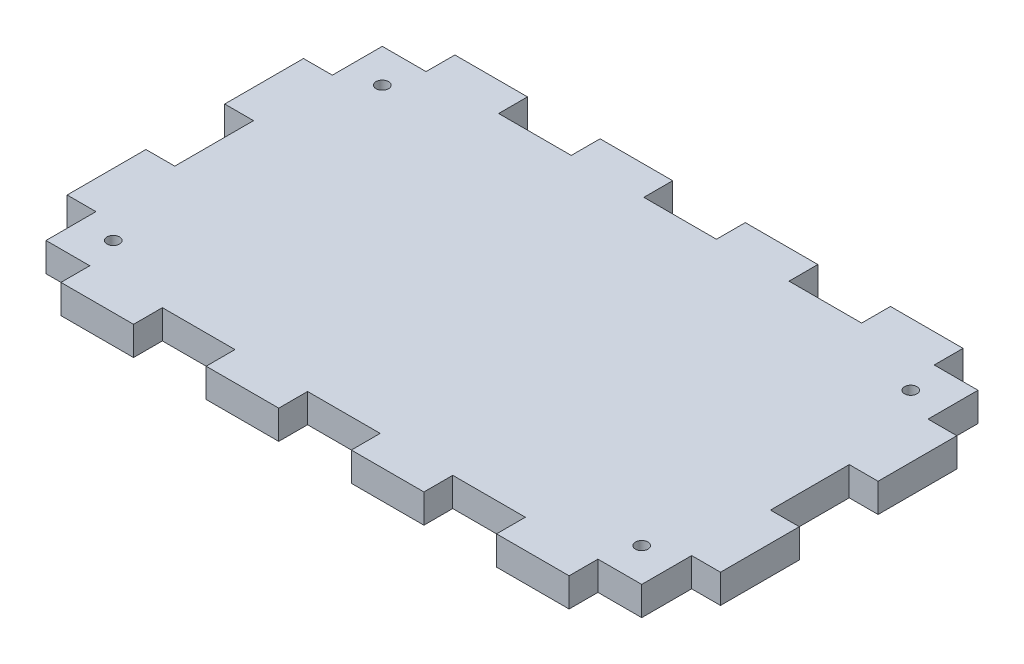
SolidWorks part; units mm, degrees
ref_plane "Front" through (0, 0, 0) normal (0, 0, 1) x (1, 0, 0)
ref_plane "Top" through (0, 0, 0) normal (0, 1, 0) x (1, 0, 0)
ref_plane "Right" through (0, 0, 0) normal (1, 0, 0) x (0, 0, -1)
sketch "Skizze1" plane through (0, 0, 0) normal (0, 1, 0) x (1, 0, 0)
  line L1 (0, 0) -> (68, 0) construction
  line L2 (0, 0) -> (0, 41) construction
  line L3 (0, 41) -> (68, 41) construction
  line L4 (68, 0) -> (68, 41) construction
  line L88 (3, 37.9994) -> (3, 32.8)
  line L89 (3, 32.8) -> (0, 32.8)
  line L90 (0, 32.8) -> (0, 24.5991)
  line L91 (3, 24.5991) -> (0, 24.5991)
  line L92 (3, 24.5991) -> (3, 16.3998)
  line L93 (3, 16.3998) -> (0, 16.3998)
  line L94 (0, 16.3998) -> (0, 8.1991)
  line L95 (3, 8.1991) -> (0, 8.1991)
  line L96 (3, 8.1991) -> (3, 3)
  line L97 (65.0006, 37.9994) -> (65.0006, 32.8)
  line L98 (68.0009, 32.8) -> (65.0006, 32.8)
  line L99 (68.0009, 32.8) -> (68.0009, 24.5991)
  line L100 (68.0009, 24.5991) -> (65.0006, 24.5991)
  line L101 (65.0006, 24.5991) -> (65.0006, 16.3998)
  line L102 (68.0009, 16.3998) -> (65.0006, 16.3998)
  line L103 (68.0009, 16.3998) -> (68.0009, 8.1991)
  line L104 (68.0009, 8.1991) -> (65.0006, 8.1991)
  line L105 (65.0006, 8.1991) -> (65.0006, 3)
  line L106 (3, 37.9994) -> (7.5557, 37.9994)
  line L107 (7.5557, 37.9994) -> (7.5557, 40.9994)
  line L108 (7.5557, 40.9994) -> (15.1117, 40.9994)
  line L109 (15.1117, 37.9994) -> (15.1117, 40.9994)
  line L110 (15.1117, 37.9994) -> (22.6675, 37.9994)
  line L111 (22.6675, 37.9994) -> (22.6675, 40.9994)
  line L112 (22.6675, 40.9994) -> (30.2232, 40.9994)
  line L113 (30.2232, 37.9994) -> (30.2232, 40.9994)
  line L114 (30.2232, 37.9994) -> (37.7789, 37.9994)
  line L115 (37.7789, 37.9994) -> (37.7789, 40.9994)
  line L116 (37.7789, 40.9994) -> (45.3334, 40.9994)
  line L117 (45.3334, 37.9994) -> (45.3334, 40.9994)
  line L118 (45.3334, 37.9994) -> (52.8892, 37.9994)
  line L119 (52.8892, 37.9994) -> (52.8892, 40.9994)
  line L120 (52.8892, 40.9994) -> (60.4449, 40.9994)
  line L121 (60.4449, 37.9994) -> (60.4449, 40.9994)
  line L122 (60.4449, 37.9994) -> (65.0006, 37.9994)
  line L123 (3, 3) -> (7.5557, 3)
  line L124 (7.5557, 0) -> (7.5557, 3)
  line L125 (7.5557, 0) -> (15.1117, 0)
  line L126 (15.1117, 0) -> (15.1117, 3)
  line L127 (15.1117, 3) -> (22.6675, 3)
  line L128 (22.6675, 0) -> (22.6675, 3)
  line L129 (22.6675, 0) -> (30.2232, 0)
  line L130 (30.2232, 0) -> (30.2232, 3)
  line L131 (30.2232, 3) -> (37.7789, 3)
  line L132 (37.7789, 0) -> (37.7789, 3)
  line L133 (37.7789, 0) -> (45.3334, 0)
  line L134 (45.3334, 0) -> (45.3334, 3)
  line L135 (45.3334, 3) -> (52.8891, 3)
  line L136 (52.8891, 0) -> (52.8891, 3)
  line L137 (52.8891, 0) -> (60.4449, 0)
  line L138 (60.4449, 0) -> (60.4449, 3)
  line L139 (60.4449, 3) -> (65.0006, 3)
  dimension "D1" = 68
  dimension "D2" = 41
extrude "Aufsatz-Linear austragen1" add sketch "Skizze1" along normal blind 3
sketch "Skizze2" plane through (0, 3, 0) normal (0, 1, 0) x (1, 0, 0)
  line L0 (3, 20.4995) -> (6.5011, 20.4995) construction
  line L1 (6.5011, 34.4995) -> (61.5011, 34.4995) construction
  line L2 (6.5011, 34.4995) -> (6.5011, 6.4995) construction
  line L3 (6.5011, 6.4995) -> (61.5011, 6.4995) construction
  line L4 (61.5011, 34.4995) -> (61.5011, 6.4995) construction
  line L5 (3, 24.5991) -> (3, 16.3998) construction
  line L6 (34.0011, 37.9994) -> (34.0011, 34.4995) construction
  line L7 (37.7789, 37.9994) -> (30.2232, 37.9994) construction
  circle A0 centre (6.5011, 34.4995) radius 0.65
  circle A1 centre (61.5011, 34.4995) radius 0.65
  circle A2 centre (61.5011, 6.4995) radius 0.65
  circle A3 centre (6.5011, 6.4995) radius 0.65
  dimension "D1" = 1.3
  dimension "D2" = 28
  dimension "D3" = 55
extrude "Schnitt-Linear austragen1" cut sketch "Skizze2" against normal up to next
sketch "Skizze3" [suppressed] plane through (0, 3, 0) normal (0, 1, 0) x (1, 0, 0)
  line L0 (65.0006, 32.8) -> (65.0006, 37.9994) construction
  line L1 (37.7789, 37.9994) -> (30.2232, 37.9994) construction
  line L2 (65.0006, 3) -> (65.0006, 8.1991) construction
  line L5 (45.3334, 3) -> (52.8891, 3) construction
  circle A0 centre (39.0006, 35.4994) radius 1.75
  circle A1 centre (52.5006, 7) radius 2.1
  circle A2 centre (14.0006, 7) radius 2.1
  dimension "D1" = 26
  dimension "D2" = 3.5
  dimension "D4" = 4.2
  dimension "D3" = 2.5
  dimension "D5" = 12.5
  dimension "D6" = 4
  dimension "D7" = 38.5
extrude "Schnitt-Linear austragen2" [suppressed] cut sketch "Skizze3" against normal up to next
equation "\"D4@Skizze4\"=\"D1@Skizze4\""
